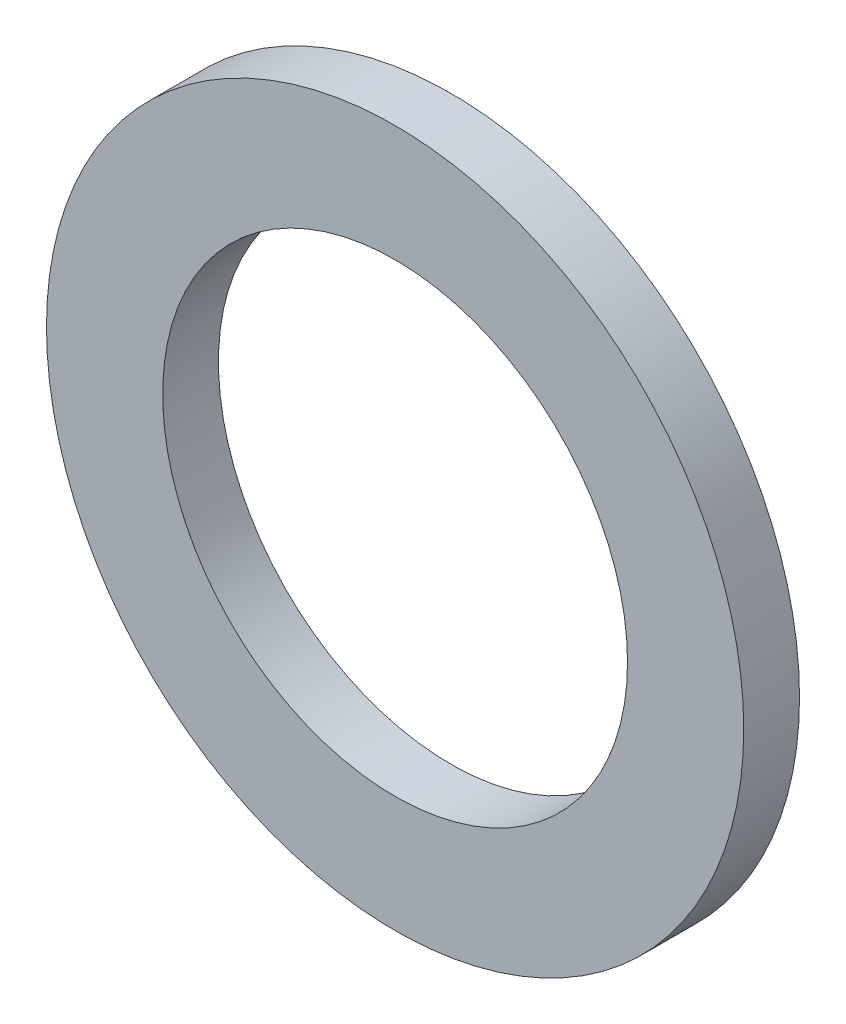
SolidWorks part; units mm, degrees
material "AISI 316 Stainless Steel Sheet (SS)"
ref_plane "Front Plane" through (0, 0, 0) normal (0, 0, 1) x (1, 0, 0)
ref_plane "Top Plane" through (0, 0, 0) normal (0, 1, 0) x (1, 0, 0)
ref_plane "Right Plane" through (0, 0, 0) normal (1, 0, 0) x (0, 0, -1)
sketch "Sketch1" plane through (0, 0, 0) normal (0, 0, 1) x (1, 0, 0)
  circle A0 centre (0, 0) radius 3.175
  circle A1 centre (0, 0) radius 4.7625
  dimension "D1" = 6.35
  dimension "D2" = 9.525
extrude "Boss-Extrude1" add sketch "Sketch1" along normal blind 0.762
